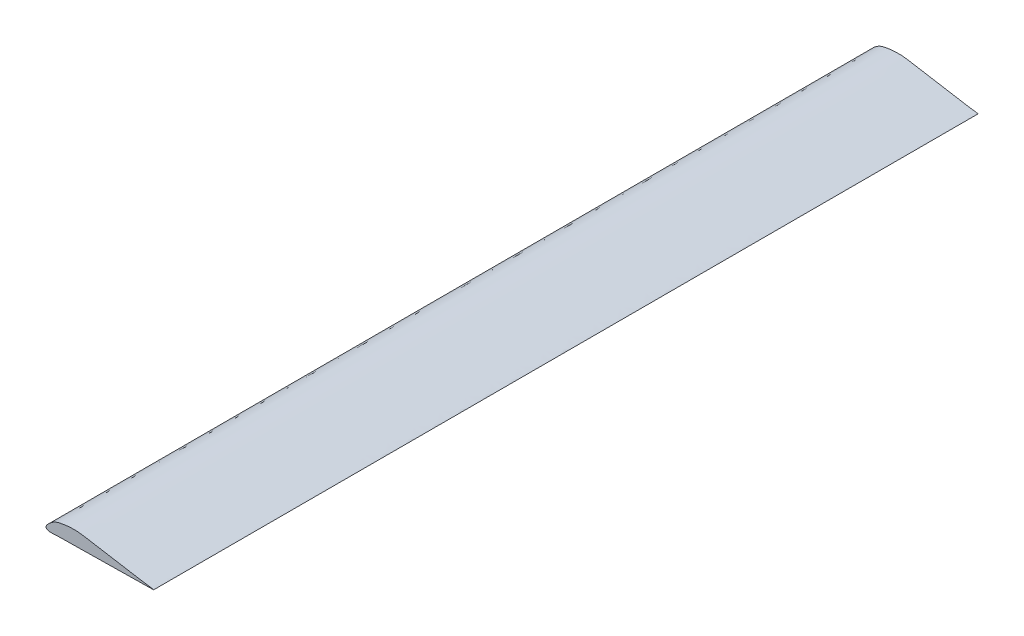
SolidWorks part; units mm, degrees
ref_plane "Front Plane" through (0, 0, 0) normal (0, 0, 1) x (1, 0, 0)
ref_plane "Top Plane" through (0, 0, 0) normal (0, 1, 0) x (1, 0, 0)
ref_plane "Right Plane" through (0, 0, 0) normal (1, 0, 0) x (0, 0, -1)
curve "Curve1"
  spline degree 3 poles (23.3936, -0.0091, 0) (26.5421, -0.0724, 0) (22.846, 0.3911, 0) (21.1467, 0.7182, 0) (18.8415, 1.0905, 0) (16.6987, 1.4511, 0) (14.5123, 1.8136, 0) (12.3379, 2.1801, 0) (10.0402, 2.548, 0) (7.9315, 2.9561, 0) (5.877, 2.9795, 0) (4.0472, 2.7683, 0) (2.4121, 2.4386, 0) (1.3547, 1.792, 0) (0.8323, 1.347, 0) (0.4716, 0.9793, 0) (0.1356, 0.6323, 0) (-0.1448, 0.0575, 0) (0.2731, -0.3048, 0) (1.1151, -0.4813, 0) (2.4547, -0.3119, 0) (4.2154, -0.3378, 0) (5.982, -0.2963, 0) (7.7469, -0.2729, 0) (9.5123, -0.2447, 0) (11.2776, -0.2178, 0) (13.0428, -0.1905, 0) (14.8085, -0.1633, 0) (16.5723, -0.136, 0) (18.3434, -0.1092, 0) (20.0868, -0.0803, 0) (21.934, -0.0593, 0) (23.3936, -0.0091, 0) (26.5421, -0.0724, 0) (22.846, 0.3911, 0) knots -0.101253 -0.067502 -0.033751 0 0.042194 0.084388 0.126583 0.168777 0.210971 0.253165 0.295359 0.344459 0.376025 0.412649 0.450339 0.470158 0.482904 0.489771 0.499409 0.512015 0.518882 0.527487 0.561238 0.594988 0.628739 0.66249 0.696241 0.729992 0.763743 0.797494 0.831245 0.864996 0.898747 0.932498 0.966249 1 1.042194 1.084388 1.126583 periodic
sketch "Sketch1" plane through (0, 0, 0) normal (0, 0, 1) x (1, 0, 0)
  line L0 (0, 0) -> (76.2, 0) construction
  line L1 (38.1, 0) -> (38.1, 6.3518) construction
  spline S0 degree 3 poles (23.3936, -0.0091) (26.5421, -0.0724) (22.846, 0.3911) (21.1467, 0.7182) (18.8415, 1.0905) (16.6987, 1.4511) (14.5123, 1.8136) (12.3379, 2.1801) (10.0402, 2.548) (7.9315, 2.9561) (5.877, 2.9795) (4.0472, 2.7683) (2.4121, 2.4386) (1.3547, 1.792) (0.8323, 1.347) (0.4716, 0.9793) (0.1356, 0.6323) (-0.1448, 0.0575) (0.2731, -0.3048) (1.1151, -0.4813) (2.4547, -0.3119) (4.2154, -0.3378) (5.982, -0.2963) (7.7469, -0.2729) (9.5123, -0.2447) (11.2776, -0.2178) (13.0428, -0.1905) (14.8085, -0.1633) (16.5723, -0.136) (18.3434, -0.1092) (20.0868, -0.0803) (21.934, -0.0593) (23.3936, -0.0091) (26.5421, -0.0724) (22.846, 0.3911) knots -0.101253 -0.067502 -0.033751 0 0.042194 0.084388 0.126583 0.168777 0.210971 0.253165 0.295359 0.344459 0.376025 0.412649 0.450339 0.470158 0.482904 0.489771 0.499409 0.512015 0.518882 0.527487 0.561238 0.594988 0.628739 0.66249 0.696241 0.729992 0.763743 0.797494 0.831245 0.864996 0.898747 0.932498 0.966249 1 1.042194 1.084388 1.126583 only from (25.4, 0) to (25.4, 0) construction
  spline S1 degree 3 poles (23.3936, -0.0091) (26.5421, -0.0724) (22.846, 0.3911) (21.1467, 0.7182) (18.8415, 1.0905) (16.6987, 1.4511) (14.5123, 1.8136) (12.3379, 2.1801) (10.0402, 2.548) (7.9315, 2.9561) (5.877, 2.9795) (4.0472, 2.7683) (2.4121, 2.4386) (1.3547, 1.792) (0.8323, 1.347) (0.4716, 0.9793) (0.1356, 0.6323) (-0.1448, 0.0575) (0.2731, -0.3048) (1.1151, -0.4813) (2.4547, -0.3119) (4.2154, -0.3378) (5.982, -0.2963) (7.7469, -0.2729) (9.5123, -0.2447) (11.2776, -0.2178) (13.0428, -0.1905) (14.8085, -0.1633) (16.5723, -0.136) (18.3434, -0.1092) (20.0868, -0.0803) (21.934, -0.0593) (23.3936, -0.0091) (26.5421, -0.0724) (22.846, 0.3911) knots -0.101253 -0.067502 -0.033751 0 0.042194 0.084388 0.126583 0.168777 0.210971 0.253165 0.295359 0.344459 0.376025 0.412649 0.450339 0.470158 0.482904 0.489771 0.499409 0.512015 0.518882 0.527487 0.561238 0.594988 0.628739 0.66249 0.696241 0.729992 0.763743 0.797494 0.831245 0.864996 0.898747 0.932498 0.966249 1 1.042194 1.084388 1.126583 only from (25.4, 0) to (25.4, 0) construction
  spline S2 degree 3 poles (7.0181, -0.0027) (7.9626, -0.0217) (6.8538, 0.1173) (6.344, 0.2154) (5.6525, 0.3272) (5.0096, 0.4353) (4.3537, 0.5441) (3.7014, 0.654) (3.012, 0.7644) (2.3795, 0.8868) (1.7631, 0.8938) (1.2141, 0.8305) (0.7236, 0.7316) (0.4064, 0.5376) (0.2497, 0.4041) (0.1415, 0.2938) (0.0407, 0.1897) (-0.0434, 0.0172) (0.0819, -0.0914) (0.3345, -0.1444) (0.7364, -0.0936) (1.2646, -0.1013) (1.7946, -0.0889) (2.3241, -0.0819) (2.8537, -0.0734) (3.3833, -0.0653) (3.9128, -0.0571) (4.4426, -0.049) (4.9717, -0.0408) (5.503, -0.0328) (6.026, -0.0241) (6.5802, -0.0178) (7.0181, -0.0027) (7.9626, -0.0217) (6.8538, 0.1173) knots -0.101253 -0.067502 -0.033751 0 0.042194 0.084388 0.126583 0.168777 0.210971 0.253165 0.295359 0.344459 0.376025 0.412649 0.450339 0.470158 0.482904 0.489771 0.499409 0.512015 0.518882 0.527487 0.561238 0.594988 0.628739 0.66249 0.696241 0.729992 0.763743 0.797494 0.831245 0.864996 0.898747 0.932498 0.966249 1 1.042194 1.084388 1.126583 only from (7.62, 0) to (7.62, 0) construction
  spline S3 degree 3 poles (70.1808, -0.0274) (79.6263, -0.2171) (68.5381, 1.1733) (63.44, 2.1545) (56.5245, 3.2716) (50.0961, 4.3533) (43.5369, 5.4409) (37.0137, 6.5402) (30.1205, 7.6441) (23.7946, 8.8682) (17.6309, 8.9384) (12.1415, 8.3049) (7.2364, 7.3158) (4.0642, 5.3761) (2.4969, 4.0409) (1.4147, 2.9379) (0.4067, 1.8969) (-0.4343, 0.1725) (0.8192, -0.9145) (3.3454, -1.444) (7.364, -0.9357) (12.6463, -1.0134) (17.9459, -0.889) (23.2408, -0.8188) (28.5369, -0.7341) (33.8329, -0.6533) (39.1284, -0.5714) (44.4256, -0.4899) (49.7168, -0.4079) (55.0303, -0.3276) (60.2604, -0.241) (65.802, -0.1778) (70.1808, -0.0274) (79.6263, -0.2171) (68.5381, 1.1733) knots -0.101253 -0.067502 -0.033751 0 0.042194 0.084388 0.126583 0.168777 0.210971 0.253165 0.295359 0.344459 0.376025 0.412649 0.450339 0.470158 0.482904 0.489771 0.499409 0.512015 0.518882 0.527487 0.561238 0.594988 0.628739 0.66249 0.696241 0.729992 0.763743 0.797494 0.831245 0.864996 0.898747 0.932498 0.966249 1 1.042194 1.084388 1.126583 only from (76.2, 0) to (76.2, 0)
  dimension "D1" = 76.2
  dimension "D2" = 6.3518
extrude "Boss-Extrude1" add sketch "Sketch1" along normal blind 584.2
ref_plane "Plane1" through (0, 0, 292.1) normal (0, 0, 1) x (1, 0, 0)
sketch "Sketch2" plane through (0, 0, 292.1) normal (0, 0, 1) x (1, 0, 0)
  line L0 (0, 0) -> (0, -27.7876) construction
  line L1 (0, -27.7876) -> (7.62, -27.7876) construction
  circle A0 centre (7.62, -27.7876) radius 1.27 construction
  dimension "D3" = 2.54
  dimension "D1" = 27.7876
  dimension "D2" = 7.62
